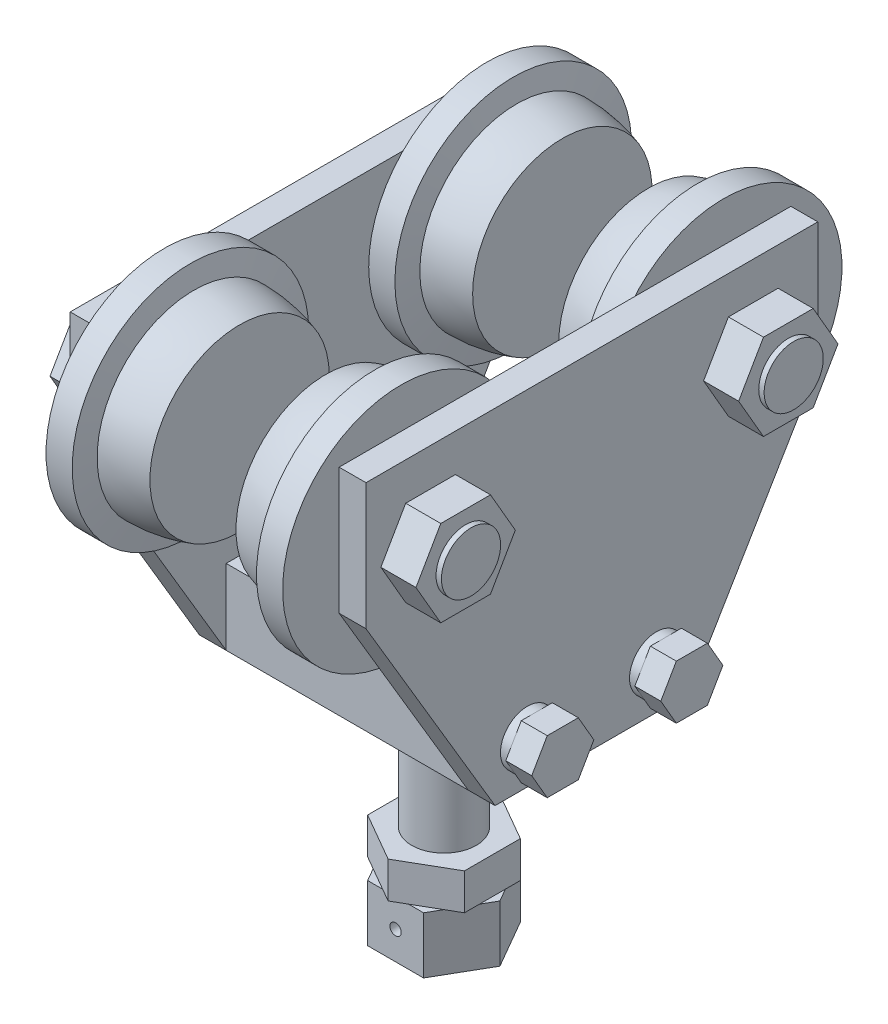
SolidWorks part; units mm, degrees
ref_plane "Front" through (0, 0, 0) normal (0, 0, 1) x (1, 0, 0)
ref_plane "Top" through (0, 0, 0) normal (0, 1, 0) x (1, 0, 0)
ref_plane "Right" through (0, 0, 0) normal (1, 0, 0) x (0, 0, -1)
ref_plane "Z PLANE" through (0, 0, 0) normal (0, 0, 1) x (1, 0, 0)
ref_plane "YOKE BOTTOM" through (0, 0, 0) normal (0, 1, 0) x (-1, 0, 0)
ref_plane "X PLANE" through (0, 0, 0) normal (1, 0, 0) x (0, 0, -1)
sketch "YOKE CROSS SECTION" plane through (0, 0, 0) normal (1, 0, 0) x (0, 0, -1)
  line L0 (0, 0) -> (0, 57.0916) construction
  line L1 (0, 84.8167) -> (0, -84.8167) construction
  line L2 (-57.15, 0) -> (57.15, 0)
  line L3 (69.1602, 0) -> (-69.1602, 0) construction
  line L4 (57.15, 0) -> (57.15, 44.45)
  line L5 (-57.15, 0) -> (-57.15, 44.45)
  line L6 (57.15, 44.45) -> (-57.15, 44.45)
  point P12 (0, 44.45)
  dimension "D1" = 44.45
  dimension "D2" = 114.3
ref_plane "1/2 YOKE LENGTH (A)" through (71.4375, 0, 0) normal (1, 0, 0) x (0, 0, -1)
ref_plane "WHEEL LOCATION" through (0, 0, 95.25) normal (0, 0, 1) x (1, 0, 0)
extrude "YOKE" add sketch "YOKE CROSS SECTION" along normal up to surface (71.4375 mm away) up to plane "1/2 YOKE LENGTH (A)"
sketch "SIDEPLATE PROFILE" plane through (71.4375, 0, 0) normal (1, 0, 0) x (0, 0, -1)
  line L0 (-133.35, 203.2) -> (-133.35, 128.5178)
  line L1 (0, 84.8167) -> (0, -84.8167) construction
  line L2 (133.35, 203.2) -> (133.35, 128.5178)
  line L3 (0, 0) -> (-57.15, 0)
  line L4 (-133.35, 128.5178) -> (-57.15, 0)
  line L5 (133.35, 128.5178) -> (57.15, 0)
  line L6 (0, 0) -> (57.15, 0)
  line L7 (-133.35, 203.2) -> (133.35, 203.2)
  line L8 (69.1602, 0) -> (-69.1602, 0) construction
  dimension "D1" = 57.15
  dimension "D2" = 76.2
  dimension "D3" = 76.2
  dimension "D4" = 57.15
  dimension "D5" = 76.2
  dimension "D6" = 76.2
  dimension "D7" = 266.7
  dimension "D8" = 128.5178
  dimension "D9" = 128.5178
  dimension "D10" = 203.2
ref_plane "WHEEL HEIGHT" through (0, 155.575, 0) normal (0, 1, 0) x (-1, 0, 0)
ref_plane "YOKE SCREW LOCATION Z" through (0, 0, 38.1) normal (0, 0, 1) x (1, 0, 0)
ref_plane "YOKE SCREW LOCATION Y" through (0, 25.4, 0) normal (0, 1, 0) x (-1, 0, 0)
extrude "SIDEPLATE" add sketch "SIDEPLATE PROFILE" along normal blind 15.875
sketch "WHEEL PIN NUT PROFILE" plane through (87.3125, 0, 0) normal (1, 0, 0) x (0, 0, -1)
  line L0 (-95.25, 84.8167) -> (-95.25, -84.8167) construction
  line L1 (-65.9206, 155.575) -> (-80.5853, 180.975)
  line L2 (-80.5853, 180.975) -> (-109.9147, 180.975)
  line L3 (-109.9147, 180.975) -> (-124.5794, 155.575)
  line L4 (-124.5794, 155.575) -> (-109.9147, 130.175)
  line L5 (-109.9147, 130.175) -> (-80.5853, 130.175)
  line L6 (-80.5853, 130.175) -> (-65.9206, 155.575)
  line L7 (69.1602, 155.575) -> (-69.1602, 155.575) construction
  circle A0 centre (-95.25, 155.575) radius 13.4938 construction
  dimension "D1" = 50.8
extrude "WHEEL PIN NUT" add sketch "WHEEL PIN NUT PROFILE" along normal blind 20.701
sketch "WHEEL PIN PROJECTION PROFILE" plane through (108.0135, 0, 0) normal (1, 0, 0) x (0, 0, -1)
  line L0 (-95.25, 84.8167) -> (-95.25, -84.8167) construction
  line L3 (69.1602, 155.575) -> (-69.1602, 155.575) construction
  circle A0 centre (-95.25, 155.575) radius 17.4625
  dimension "D1" = 34.925
extrude "WHEEL PIN PROJECTION" add sketch "WHEEL PIN PROJECTION PROFILE" along normal blind 3.175
sketch "LOCKNUTS PROFILE" plane through (87.3125, 0, 0) normal (1, 0, 0) x (0, 0, -1)
  line L0 (-38.1, 84.8167) -> (-38.1, -84.8167) construction
  line L1 (50, 25.4) -> (-50, 25.4) construction
  circle A0 centre (-38.1, 25.4) radius 15.875
  dimension "D1" = 31.75
extrude "LOCKNUTS" add sketch "LOCKNUTS PROFILE" along normal blind 5.5626
sketch "SCREWS PROFILE" plane through (92.8751, 0, 0) normal (1, 0, 0) x (0, 0, -1)
  line L0 (50, 25.4) -> (-50, 25.4) construction
  line L1 (-19.7691, 25.4) -> (-28.9346, 41.275)
  line L2 (-28.9346, 41.275) -> (-47.2654, 41.275)
  line L3 (-47.2654, 41.275) -> (-56.4309, 25.4)
  line L4 (-56.4309, 25.4) -> (-47.2654, 9.525)
  line L5 (-47.2654, 9.525) -> (-28.9346, 9.525)
  line L6 (-28.9346, 9.525) -> (-19.7691, 25.4)
  line L7 (-38.1, 84.8167) -> (-38.1, -84.8167) construction
  circle A0 centre (-38.1, 25.4) radius 15.875 construction
  dimension "D1" = 31.75
extrude "SCREWS" add sketch "SCREWS PROFILE" along normal blind 15.3416
sketch "PROFILE" plane through (0, 44.45, 0) normal (0, 1, 0) x (-1, 0, 0)
  line L0 (84.8167, 0) -> (-84.8167, 0) construction
  line L1 (0, 83.2389) -> (0, -83.2389) construction
  circle A0 centre (0, 0) radius 28.575
  dimension "D1" = 57.15
extrude "KING BOLT HEAD" add sketch "PROFILE" along normal blind 31.75
mirror "Mirror1" about plane through (0, 0, 0) normal (0, 0, 1) of "WHEEL PIN PROJECTION", "WHEEL PIN NUT"
mirror "Mirror YOKE SCREWS" about plane through (0, 0, 0) normal (0, 0, 1) of "SCREWS", "LOCKNUTS"
mirror "Mirror SIDE 1" about plane through (0, 0, 0) normal (1, 0, 0) of bodies 112
ref_plane "TOP OF NUT" through (0, -83.0521, 0) normal (0, 1, 0) x (-1, 0, 0)
sketch "DIA." plane through (0, 0, 0) normal (0, -1, 0) x (1, 0, 0)
  line L0 (84.8167, 0) -> (-84.8167, 0) construction
  line L1 (0, -83.2389) -> (0, 83.2389) construction
  circle A0 centre (0, 0) radius 19.05
  dimension "D1" = 38.1
extrude "KING BOLT" add sketch "DIA." along normal up to surface (83.0521 mm away) up to plane "TOP OF NUT"
sketch "KING BOLT JAN NUT PROFILE" plane through (0, -83.0521, 0) normal (0, -1, 0) x (1, 0, 0)
  line L0 (84.8167, 0) -> (-84.8167, 0) construction
  line L1 (0, -32.9956) -> (28.575, -16.4978)
  line L2 (28.575, -16.4978) -> (28.575, 16.4978)
  line L3 (28.575, 16.4978) -> (0, 32.9956)
  line L4 (0, 32.9956) -> (-28.575, 16.4978)
  line L5 (-28.575, 16.4978) -> (-28.575, -16.4978)
  line L6 (-28.575, -16.4978) -> (0, -32.9956)
  line L7 (0, -83.2389) -> (0, 83.2389) construction
  circle A0 centre (0, 0) radius 28.575 construction
  dimension "D1" = 57.15
extrude "KING BOLT JAM NUT" add sketch "KING BOLT JAN NUT PROFILE" along normal blind 21.4312
sketch "KING BOLT NUT PROFILE" plane through (0, -104.4834, 0) normal (0, -1, 0) x (1, 0, 0)
  line L1 (32.9956, 0) -> (16.4978, 28.575)
  line L2 (16.4978, 28.575) -> (-16.4978, 28.575)
  line L3 (-16.4978, 28.575) -> (-32.9956, 0)
  line L4 (-32.9956, 0) -> (-16.4978, -28.575)
  line L5 (-16.4978, -28.575) -> (16.4978, -28.575)
  line L6 (16.4978, -28.575) -> (32.9956, 0)
  line L10 (0, -83.2389) -> (0, 83.2389) construction
  line L11 (84.8167, 0) -> (-84.8167, 0) construction
  circle A0 centre (0, 0) radius 28.575 construction
  dimension "D1" = 57.15
extrude "KING BOLT NUT" add sketch "KING BOLT NUT PROFILE" along normal blind 33.3375
sketch "Sketch5" plane through (0, -137.8209, 0) normal (0, -1, 0) x (1, 0, 0)
  circle A0 centre (0, 0) radius 19.05 construction
  circle A1 centre (0, 0) radius 19.05
extrude "EXTENDED KING BOLT" add sketch "Sketch5" along normal blind 6.35
chamfer "Chamfer1" distance 2.3812 angle 45 1 edges at (0, -144.1709, -19.05)
ref_plane "MOUNTING REF PLANE" through (0, -34.925, 0) normal (0, 1, 0) x (-1, 0, 0)
sketch "Sketch11" plane through (0, 0, -28.575) normal (0, 0, -1) x (-1, 0, 0)
  line L1 (16.4978, -137.8209) -> (-16.4978, -137.8209) construction
  line L2 (0, 83.2389) -> (0, -83.2389) construction
  circle A0 centre (0, -121.1521) radius 3.3401
  point P4 (0, -137.8209)
  dimension "D1" = 6.6802
  dimension "D2" = 16.6687
extrude "COTTER PIN HOLE" cut sketch "Sketch11" against normal up to next
sketch "Sketch12" plane through (0, 0, 95.25) normal (0, 0, 1) x (1, 0, 0)
  line L0 (25.4, 155.575) -> (25.4, 208.5297)
  line L1 (69.85, 179.3875) -> (69.85, 225.425)
  line L2 (71.4375, 155.575) -> (71.4375, 179.3875)
  line L3 (25.4, 155.575) -> (71.4375, 155.575)
  line L4 (71.4375, 179.3875) -> (69.85, 179.3875)
  line L5 (69.85, 225.425) -> (54.399, 225.425)
  line L6 (52.3875, 212.725) -> (54.399, 225.425)
  line L8 (69.1602, 155.575) -> (-69.1602, 155.575) construction
  line L9 (71.4375, -75.0522) -> (71.4375, 75.0522) construction
  arc A0 (52.3875, 212.725) -> (25.4, 208.5297) centre (52.3875, 123.825) ccw
  dimension "D12" = 88.9
  dimension "D1" = 1.5875
  dimension "D2" = 46.0375
  dimension "D3" = 1.5875
  dimension "D4" = 17.0385
  dimension "D5" = 19.05
  dimension "D6" = 46.0375
  dimension "D7" = 23.8125
  dimension "D8" = 69.85
  dimension "D9" = 69.85
  dimension "D10" = 57.15
  dimension "D11" = 52.9547
revolve "WHEEL" add sketch "Sketch12" angle 360 about axis through (111.1885, 155.575, 95.25) along (-1, 0, 0)
mirror "Mirror2" about plane through (0, 0, 0) normal (0, 0, 1) of "WHEEL"
mirror "Mirror3" about plane through (0, 0, 0) normal (1, 0, 0) of "Mirror2", "WHEEL"
sketch "Sketch13" plane through (0, 0, 0) normal (0, -1, 0) x (1, 0, 0)
  circle A0 centre (0, 0) radius 25.4
  circle A1 centre (0, 0) radius 30.1625
  dimension "D1" = 50.8
  dimension "D2" = 60.325
extrude "SPACER" add sketch "Sketch13" along normal blind 12.7
ref_plane "TREAD OF TRACK" through (0, 98.425, 0) normal (0, 1, 0) x (-1, 0, 0)
